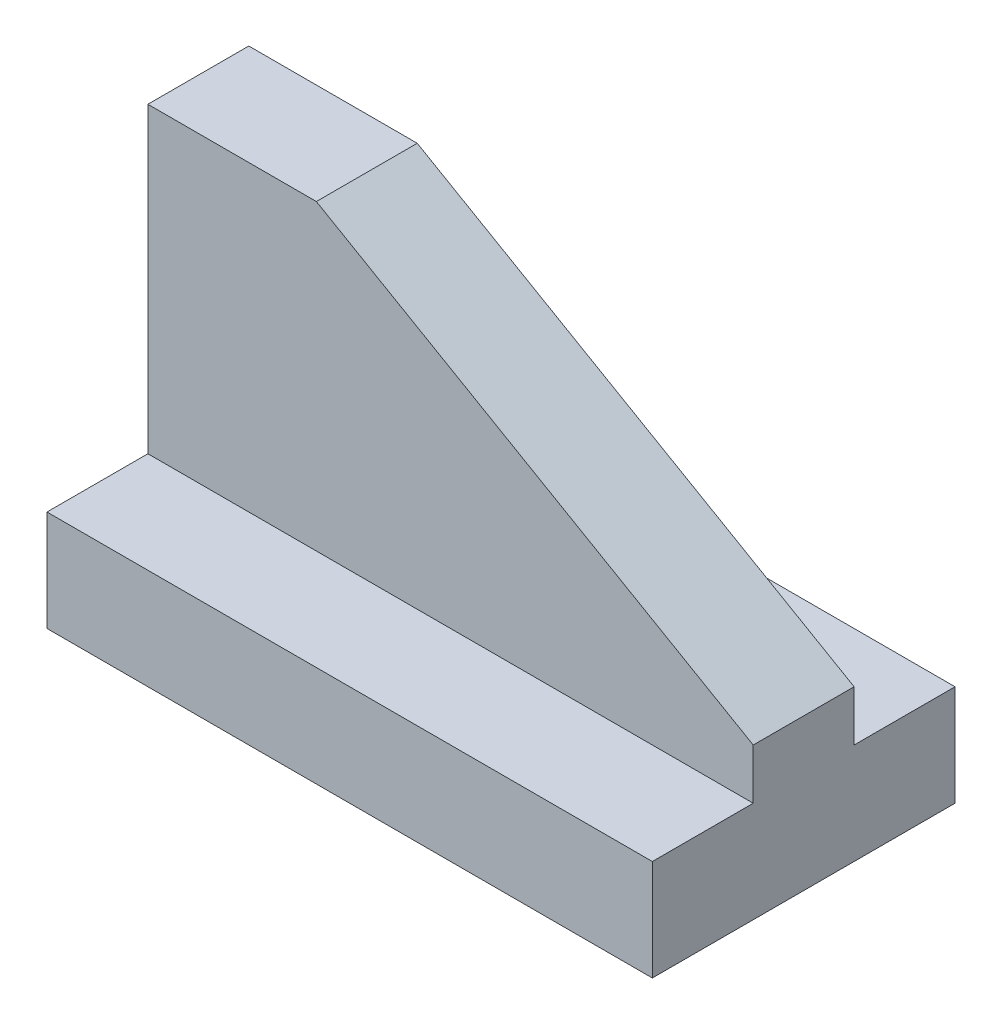
SolidWorks part; units mm, degrees
ref_plane "Front Plane" through (0, 0, 0) normal (0, 0, 1) x (1, 0, 0)
ref_plane "Top Plane" through (0, 0, 0) normal (0, 1, 0) x (1, 0, 0)
ref_plane "Right Plane" through (0, 0, 0) normal (1, 0, 0) x (0, 0, -1)
sketch "Sketch1" plane through (0, 0, 0) normal (0, 0, 1) x (1, 0, 0)
  line L1 (0, 0) -> (120, 0)
  line L2 (0, 0) -> (0, 20)
  line L3 (0, 20) -> (120, 20)
  line L4 (120, 0) -> (120, 20)
  dimension "D1" = 120
  dimension "D2" = 20
extrude "Boss-Extrude1" add sketch "Sketch1" along normal blind 60
ref_plane "Plane1" through (0, 0, 20) normal (0, 0, 1) x (1, 0, 0)
sketch "Sketch2" plane through (0, 0, 20) normal (0, 0, 1) x (1, 0, 0)
  line L0 (0, 20) -> (0, 80)
  line L1 (120, 20) -> (0, 20) construction
  line L2 (0, 80) -> (33.3975, 80)
  line L3 (33.3975, 80) -> (120, 30)
  line L4 (120, 30) -> (120, 20)
  line L5 (120, 0) -> (120, 20) construction
  line L6 (120, 20) -> (0, 20)
  dimension "D1" = 60
  dimension "D2" = 10
  dimension "D3" = 60
extrude "Boss-Extrude2" add sketch "Sketch2" along normal blind 20
